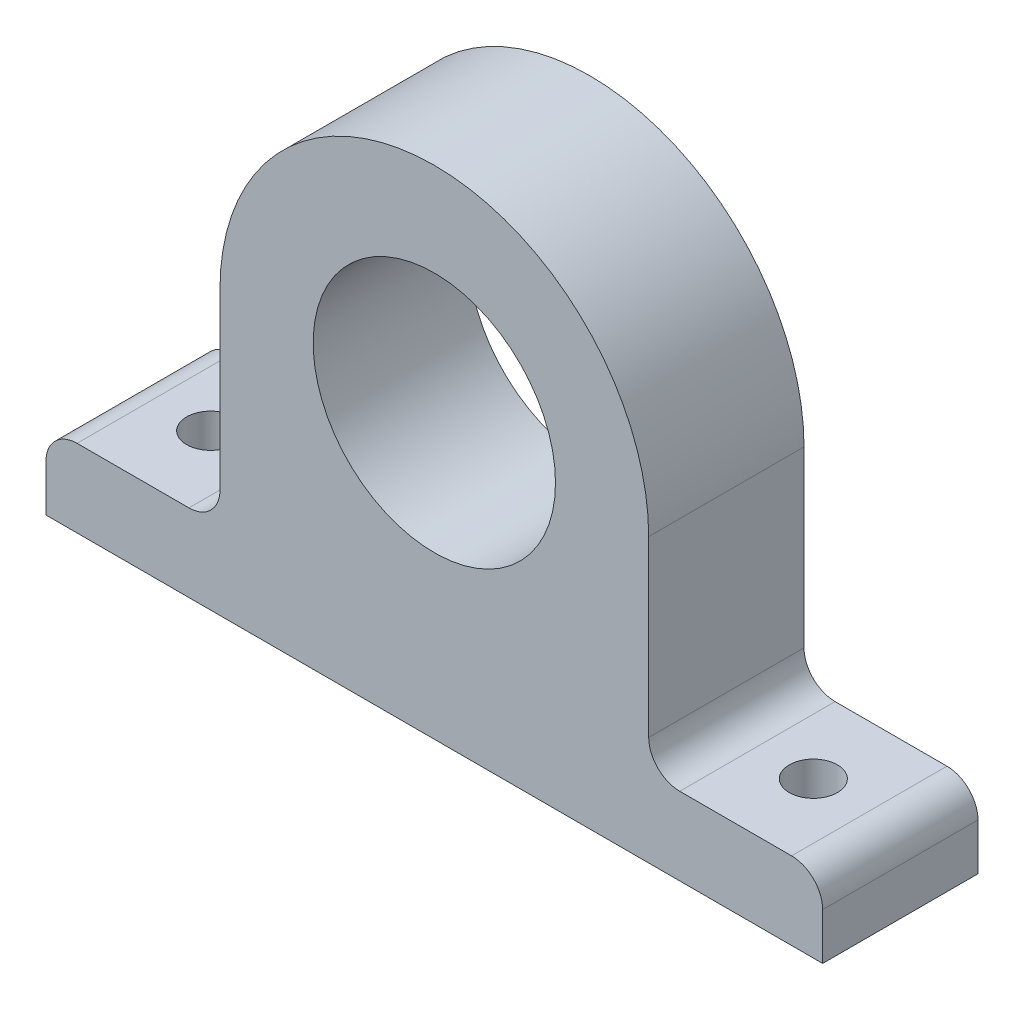
SolidWorks part; units mm, degrees
ref_plane "Front Plane" through (0, 0, 0) normal (0, 0, 1) x (1, 0, 0)
ref_plane "Top Plane" through (0, 0, 0) normal (0, 1, 0) x (1, 0, 0)
ref_plane "Right Plane" through (0, 0, 0) normal (1, 0, 0) x (0, 0, -1)
sketch "Sketch1" plane through (0, 0, 0) normal (0, 0, 1) x (1, 0, 0)
  line L0 (0, 0) -> (0, 32) construction
  line L1 (-25, 0) -> (25, 0)
  line L2 (-25, 0) -> (-25, 5)
  line L3 (-13.8, 18.2) -> (13.8, 18.2) construction
  line L4 (25, 0) -> (25, 5)
  line L5 (-25, 5) -> (-13.8, 5)
  line L6 (-13.8, 5) -> (-13.8, 18.2)
  line L7 (25, 5) -> (13.8, 5)
  line L8 (13.8, 5) -> (13.8, 18.2)
  circle A0 centre (0, 18.2) radius 7.8
  arc A1 (13.8, 18.2) -> (-13.8, 18.2) centre (0, 18.2) ccw
  circle A3 centre (0, 18.2) radius 13.8 construction
  point P13 (13.197, 22.2347)
  dimension "D3" = 15.6
  dimension "D1" = 5
  dimension "D2" = 50
  dimension "D5" = 32
  dimension "D6" = 5
  dimension "D4" = 6
extrude "Boss-Extrude1" add sketch "Sketch1" against normal blind 10
sketch "Sketch2" plane through (0, 5, 0) normal (0, 1, 0) x (1, 0, 0)
  line L0 (-25, 5) -> (-13.8, 5) construction
  line L1 (-25, 10) -> (-25, 0) construction
  line L2 (-13.8, 10) -> (-13.8, 0) construction
  circle A0 centre (-19.4, 5) radius 1.55
  point P6 (-19.4, 5)
  dimension "D1" = 3.1
extrude "Cut-Extrude1" cut sketch "Sketch2" against normal up to next (5 mm away)
mirror "Mirror1" about plane through (0, 0, 0) normal (1, 0, 0) of "Cut-Extrude1"
fillet "Fillet1" radius 2 4 edges at (13.8, 5, -5) (-13.8, 5, -5) (25, 5, -5) (-25, 5, -5)
